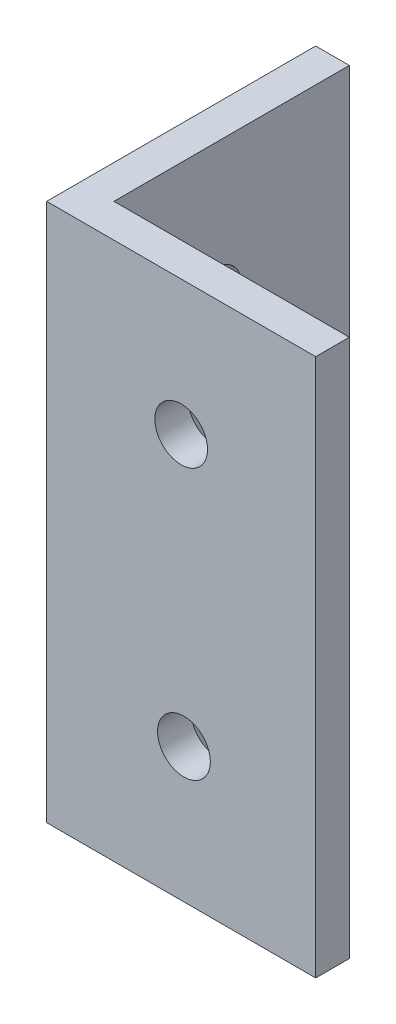
SolidWorks part; units mm, degrees
ref_plane "Front Plane" through (0, 0, 0) normal (0, 0, 1) x (1, 0, 0)
ref_plane "Top Plane" through (0, 0, 0) normal (0, 1, 0) x (1, 0, 0)
ref_plane "Right Plane" through (0, 0, 0) normal (1, 0, 0) x (0, 0, -1)
sketch "Sketch1" plane through (0, 0, 0) normal (0, 1, 0) x (1, 0, 0)
  line L0 (0, 0) -> (0, 25.4)
  line L1 (0, 0) -> (25.4, 0)
  dimension "D1" = 25.4
extrude "Extrude-Thin1" add sketch "Sketch1" along normal blind 50.8 thin
ref_plane "Plane1" through (0, 0, 0) normal (-0.7071, 0, -0.7071) x (-0.7071, 0, 0.7071)
hole_wizard "#9 (0.196) Diameter Hole1" positions "Sketch3" profile "Sketch4" hole size "#9" standard "ANSI Inch" end condition up to next
sketch "Sketch3" plane through (0, 0, -3.175) normal (0, 0, -1) x (-1, 0, 0)
  line L0 (-25.4, 50.8) -> (-25.4, 0) construction
  line L1 (-3.175, 50.8) -> (-25.4, 50.8) construction
  point P0 (-12.9602, 12.7)
  point P2 (-12.7, 38.1)
  dimension "D1" = 12.7
  dimension "D2" = 12.7
  dimension "D3" = 25.4
sketch "Sketch4" plane through (12.9602, 12.7, -3.175) normal (1, 0, 0) x (0, 1, 0)
  line L0 (0, 0) -> (0, 3.176)
  line L1 (0, 3.176) -> (2.4892, 3.176)
  line L2 (2.4892, 3.176) -> (2.4892, 0)
  line L5 (2.4892, 0) -> (0, 0)
  line L11 (0, -6.35) -> (0, 107.95) construction
  dimension "Thru Hole Dia." = 4.9784
  dimension "Thru Hole Depth" = 3.176
mirror "Mirror1" about plane through (0, 0, 0) normal (-0.7071, 0, -0.7071) of "#9 (0.196) Diameter Hole1"
equation "\"Thick\"= \"in\""
